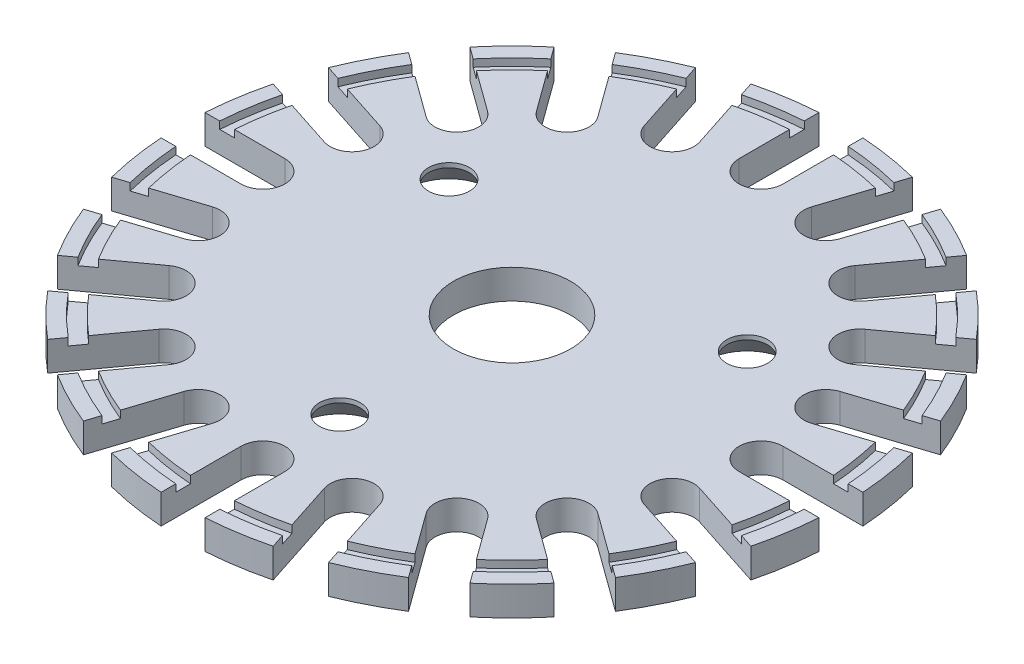
SolidWorks part; units mm, degrees
material "Alloy Steel"
ref_plane "Front Plane" through (0, 0, 0) normal (0, 0, 1) x (1, 0, 0)
ref_plane "Top Plane" through (0, 0, 0) normal (0, 1, 0) x (1, 0, 0)
ref_plane "Right Plane" through (0, 0, 0) normal (1, 0, 0) x (0, 0, -1)
sketch "Sketch1" plane through (0, 0, 0) normal (0, 1, 0) x (1, 0, 0)
  circle A0 centre (0, 0) radius 22.5
  dimension "D1" = 45
extrude "Boss-Extrude1" add sketch "Sketch1" along normal blind 2
sketch "Sketch2" plane through (0, 2, 0) normal (0, 1, 0) x (1, 0, 0)
  line L0 (0, 0) -> (0, 22.5) construction
  line L1 (0, 22.7958) -> (0, 17) construction
  line L2 (1.5, 22.7958) -> (1.5, 17)
  line L3 (-1.5, 22.7958) -> (-1.5, 17)
  circle A0 centre (0, 0) radius 22.5 construction
  arc A1 (1.5, 22.7958) -> (-1.5, 22.7958) centre (0, 22.7958) ccw
  arc A2 (-1.5, 17) -> (1.5, 17) centre (0, 17) ccw
  point P8 (0, 19.8979)
  point P14 (0, 15.5)
  dimension "D1" = 1.5
  dimension "D2" = 7
extrude "Cut-Extrude1" cut sketch "Sketch2" against normal blind 2
pattern_circular "CirPattern1" count 20 every 18 about axis through (0, 0, 0) along (0, 1, 0) of "Cut-Extrude1"
sketch "Sketch3" plane through (0, 2, 0) normal (0, 1, 0) x (1, 0, 0)
  circle A0 centre (0, 0) radius 21.5
  circle A1 centre (0, 0) radius 20.5
  dimension "D1" = 43
  dimension "D2" = 41
extrude "Cut-Extrude2" cut sketch "Sketch3" against normal blind 0.5
sketch "Sketch4" plane through (0, 2, 0) normal (0, 1, 0) x (1, 0, 0)
  circle A0 centre (0, 0) radius 4
  dimension "D1" = 8
extrude "Cut-Extrude3" cut sketch "Sketch4" against normal through all
sketch "Sketch5" plane through (0, 0, 0) normal (0, -1, 0) x (1, 0, 0)
  circle A0 centre (0, 0) radius 11.75 construction
  circle A1 centre (0, 11.75) radius 1.5
  circle A2 centre (10.1758, -5.875) radius 1.5
  circle A3 centre (-10.1758, -5.875) radius 1.5
  point P11 (0, 0)
  dimension "D1" = 23.5
  dimension "D2" = 3
  dimension "D3" = 3
hole_wizard "CSK for #3 Flat Head Socket Cap Screw1" positions "3DSketch1" profile "Sketch6" countersink size "#3" standard "ANSI Inch"
sketch3d "3DSketch1"
  point P0 (0, 0, 11.75)
  point P3 (-10.1758, 0, -5.875)
  point P6 (10.1758, 0, -5.875)
  point P9 (-99.3803, 0, 29.5597)
sketch "Sketch6" plane through (0, 0, 11.75) normal (1, 0, 0) x (0, 0, -1)
  line L0 (0, 0) -> (0, 6.3394)
  line L1 (0, 6.3394) -> (1.397, 5.5)
  line L2 (1.397, 5.5) -> (1.397, 1.6947)
  line L3 (1.397, 1.6947) -> (2.8702, 0)
  line L5 (2.8702, 0) -> (0, 0)
  line L6 (-1.397, 1.6947) -> (-2.8702, 0) construction
  line L10 (0, 6.3394) -> (-1.397, 5.5) construction
  line L11 (0, -6.35) -> (0, 107.95) construction
  dimension "Hole Dia." = 2.794
  dimension "Hole Depth" = 5.5
  dimension "Near C'Sink Dia." = 5.7404
  dimension "Near C'Sink Angle" = 82
  dimension "Drill Angle" = 118
